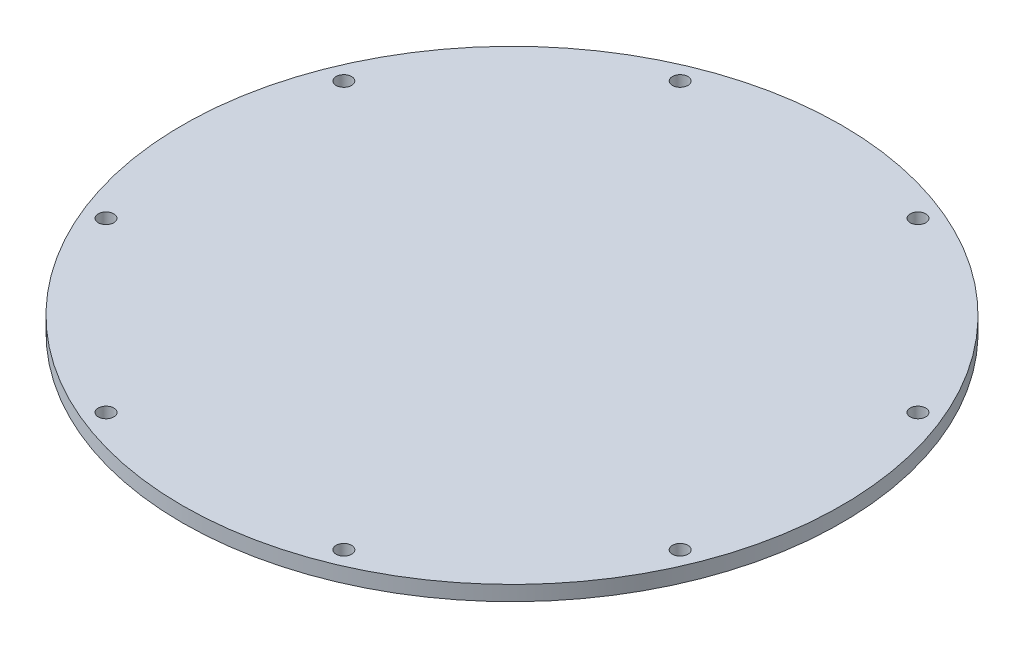
SolidWorks part; units mm, degrees
ref_plane "Front Plane" through (0, 0, 0) normal (0, 0, 1) x (1, 0, 0)
ref_plane "Top Plane" through (0, 0, 0) normal (0, 1, 0) x (1, 0, 0)
ref_plane "Right Plane" through (0, 0, 0) normal (1, 0, 0) x (0, 0, -1)
sketch "Base w/ Motor Mounts" plane through (0, 0, 0) normal (0, 1, 0) x (1, 0, 0)
  line L0 (0, 70) -> (0, -70) construction
  line L1 (0, 0) -> (70, 0) construction
  circle A0 centre (0, 0) radius 70
  dimension "D6" = 140
sketch "Standoffs (top / bottom)" plane through (0, 0, 0) normal (0, 1, 0) x (1, 0, 0)
  line L0 (0, 0) -> (64.6716, 26.7878) construction
  line L1 (0, 0) -> (49.4975, 49.4975) construction
  line L2 (0, 0) -> (26.7878, 64.6716) construction
  line L3 (0, 0) -> (70, 0) construction
  line L4 (-70, 0) -> (70, 0) construction
  line L5 (0, 0) -> (64.6716, -26.7878) construction
  line L6 (0, 0) -> (49.4975, -49.4975) construction
  line L7 (0, 0) -> (26.7878, -64.6716) construction
  line L8 (0, 70) -> (0, -70) construction
  line L9 (0, 0) -> (-26.7878, -64.6716) construction
  line L10 (0, 0) -> (-49.4975, -49.4975) construction
  line L11 (0, 0) -> (-64.6716, -26.7878) construction
  line L12 (0, 0) -> (-26.7878, 64.6716) construction
  line L13 (0, 0) -> (-49.4975, 49.4975) construction
  line L14 (0, 0) -> (-64.6716, 26.7878) construction
  line L15 (25.2571, 60.976) -> (25.2571, 25.2571) construction
  circle A0 centre (0, 0) radius 70 construction
  circle A1 centre (25.2571, 60.976) radius 1.65
  circle A3 centre (60.976, 25.2571) radius 1.65
  circle A6 centre (60.976, -25.2571) radius 1.65
  circle A7 centre (25.2571, -60.976) radius 1.65
  circle A8 centre (-25.2571, -60.976) radius 1.65
  circle A9 centre (-60.976, -25.2571) radius 1.65
  circle A12 centre (-60.976, 25.2571) radius 1.65
  circle A13 centre (-25.2571, 60.976) radius 1.65
  dimension "D4" = 3.3
  dimension "D1" = 22.5
  dimension "D2" = 22.5
  dimension "D3" = 22.5
  dimension "D5" = 4
  dimension "D7" = 4
  dimension "D6" = 35.7189
sketch "Pi and Mega Standoffs" plane through (0, 0, 0) normal (0, 1, 0) x (1, 0, 0)
  line L0 (0, 70) -> (0, -70) construction
  line L1 (-38.1, 55) -> (19.9, 55) construction
  line L2 (-38.1, 55) -> (-38.1, 6) construction
  line L3 (-38.1, 6) -> (19.9, 6) construction
  line L4 (19.9, 55) -> (19.9, 6) construction
  line L5 (-38.1, 55) -> (19.9, 6) construction
  line L6 (-38.1, 6) -> (19.9, 55) construction
  line L7 (0, 0) -> (70, 0) construction
  line L8 (-38.1, -6) -> (38.1, -6) construction
  line L9 (-38.1, -6) -> (-38.1, -54.2) construction
  line L10 (-38.1, -54.2) -> (38.1, -54.2) construction
  line L11 (38.1, -6) -> (38.1, -54.2) construction
  line L12 (-38.1, -6) -> (38.1, -54.2) construction
  line L13 (-38.1, -54.2) -> (38.1, -6) construction
  circle A0 centre (-38.1, 55) radius 1.4
  circle A1 centre (19.9, 55) radius 1.4
  circle A2 centre (19.9, 6) radius 1.4
  circle A3 centre (-38.1, 6) radius 1.4
  circle A4 centre (-38.1, -54.2) radius 1.65
  circle A5 centre (-36.8, -6) radius 1.65
  circle A6 centre (38.1, -6) radius 1.65
  point P0 (-10.6204, 31.3097)
  point P11 (0, -30.1)
  dimension "D3" = 2.8
  dimension "D5" = 3.3
  dimension "D1" = 49
  dimension "D2" = 58
  dimension "D4" = 76.2
  dimension "D6" = 1.3
  dimension "D7" = 74.9
  dimension "D8" = 48.2
  dimension "D9" = 6
  dimension "D10" = 6
extrude "Boss-Extrude1" add sketch "Base w/ Motor Mounts" along normal blind 3.175
extrude "Cut-Extrude2" cut sketch "Standoffs (top / bottom)" along normal blind 3.175
equation "\"D7@Standoffs (top / bottom)\" = \"D5@Standoffs (top / bottom)\""
equation "\"D10@Pi and Mega Standoffs\"=\"D9@Pi and Mega Standoffs\""
